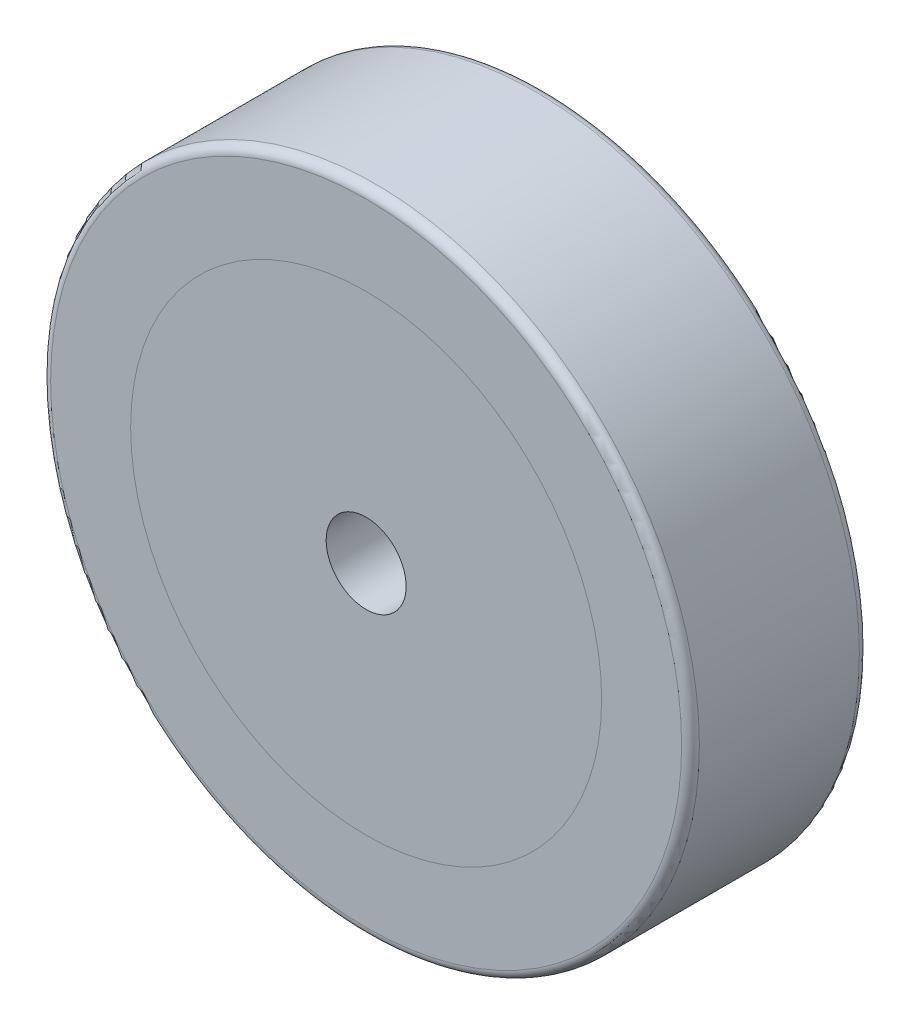
SolidWorks part; units mm, degrees
ref_plane "Plan de face" through (0, 0, 0) normal (0, 0, 1) x (1, 0, 0)
ref_plane "Plan de dessus" through (0, 0, 0) normal (0, 1, 0) x (1, 0, 0)
ref_plane "Plan de droite" through (0, 0, 0) normal (1, 0, 0) x (0, 0, -1)
sketch "Esquisse1" plane through (0, 0, 0) normal (0, 0, 1) x (1, 0, 0)
  circle A0 centre (0, 0) radius 36.5
  dimension "D1" = 73
extrude "Boss.-Extru.1" add sketch "Esquisse1" along normal blind 20
sketch "Esquisse2" plane through (0, 0, 20) normal (0, 0, 1) x (1, 0, 0)
  circle A0 centre (0, 0) radius 26.5
  dimension "D1" = 53
extrude "Enlèv. mat.-Extru.2" cut sketch "Esquisse2" against normal blind 20
sketch "Esquisse4" plane through (0, 0, 20) normal (0, 0, 1) x (1, 0, 0)
  circle A0 centre (0, 0) radius 26.5
  dimension "D1" = 53
extrude "Boss.-Extru.3" add sketch "Esquisse4" against normal blind 20 separate body
hole_wizard "Dégagement M81" positions "Esquisse10" profile "Esquisse9" hole size "M8" standard "ISO" end condition through all
sketch "Esquisse10" plane through (0, 0, 0) normal (0, 0, -1) x (-1, 0, 0)
  point P1 (0, 0)
sketch "Esquisse9" plane through (0, 0, 0) normal (1, 0, 0) x (0, 1, 0)
  line L0 (0, 0) -> (0, 20)
  line L1 (0, 20) -> (4.5, 20)
  line L2 (4.5, 20) -> (4.5, 0)
  line L5 (4.5, 0) -> (0, 0)
  line L11 (0, -6.35) -> (0, 107.95) construction
  dimension "Diamètre du perçage jusqu'au prochain" = 9
  dimension "Profondeur du perçage jusqu'au prochain" = 20
fillet "Congé1" radius 1 2 edges at (36.5, 0, 0) (36.5, 0, 20)
